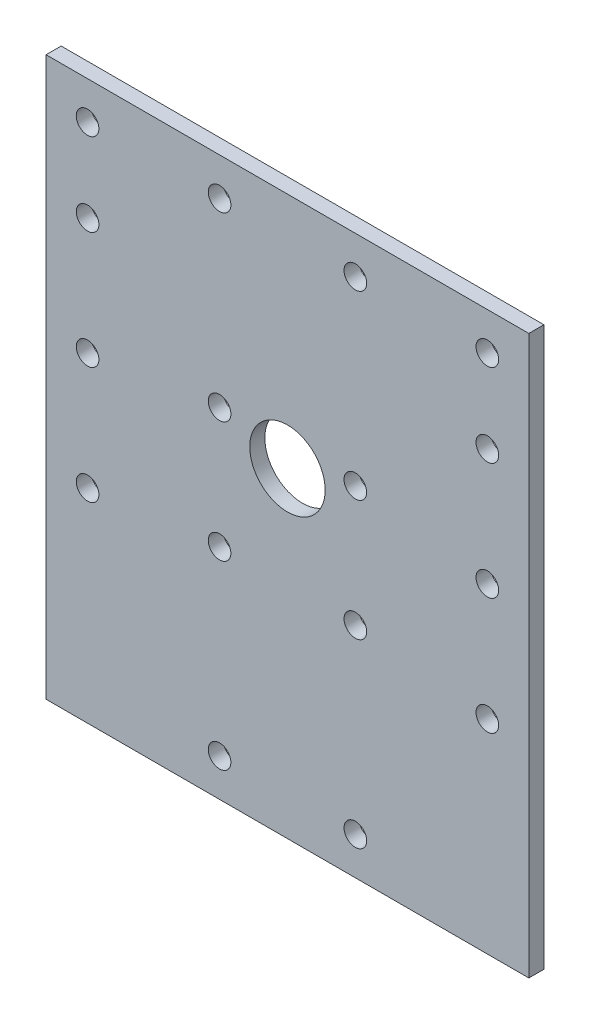
SolidWorks part; units mm, degrees
ref_plane "Front Plane" through (0, 0, 0) normal (0, 0, 1) x (1, 0, 0)
ref_plane "Top Plane" through (0, 0, 0) normal (0, 1, 0) x (1, 0, 0)
ref_plane "Right Plane" through (0, 0, 0) normal (1, 0, 0) x (0, 0, -1)
sketch "Sketch1" plane through (0, 0, 0) normal (0, 0, 1) x (1, 0, 0)
  line L1 (-32.0005, -37) -> (32.0005, -37)
  line L2 (-32.0005, -37) -> (-32.0005, 37)
  line L3 (-32.0005, 37) -> (32.0005, 37)
  line L4 (32.0005, -37) -> (32.0005, 37)
  line L5 (-32.0005, -37) -> (32.0005, 37) construction
  line L6 (-32.0005, 37) -> (32.0005, -37) construction
  line L7 (0, 0) -> (0, -34.4749) construction
  circle A0 centre (-9, 8) radius 1.5
  circle A1 centre (26.5, -10) radius 1.5
  circle A2 centre (-9, 32) radius 1.5
  circle A3 centre (-9, -32) radius 1.5
  circle A4 centre (-9, -8) radius 1.5
  circle A5 centre (26.5, 5.5) radius 1.5
  circle A6 centre (26.5, 21) radius 1.5
  circle A7 centre (26.5, 32) radius 1.5
  circle A8 centre (9, 32) radius 1.5
  circle A9 centre (9, 8) radius 1.5
  circle A10 centre (9, -8) radius 1.5
  circle A11 centre (9, -32) radius 1.5
  circle A12 centre (-26.5, -10) radius 1.5
  circle A13 centre (-26.5, 5.5) radius 1.5
  circle A14 centre (-26.5, 21) radius 1.5
  circle A15 centre (-26.5, 32) radius 1.5
  circle A16 centre (0, 5.5) radius 5
  point P0 (0, 0)
  point P6 (0, 0)
  dimension "D1" = 5
  dimension "D3" = 24
  dimension "D6" = 5
  dimension "D5" = 24
  dimension "D8" = 26.5
  dimension "D2" = 9
  dimension "D4" = 16
  dimension "D7" = 5
  dimension "D9" = 9
  dimension "D10" = 9
  dimension "D11" = 9
  dimension "D12" = 11
  dimension "D13" = 15.5
  dimension "D14" = 15.5
extrude "Boss-Extrude1" add sketch "Sketch1" along normal blind 2
